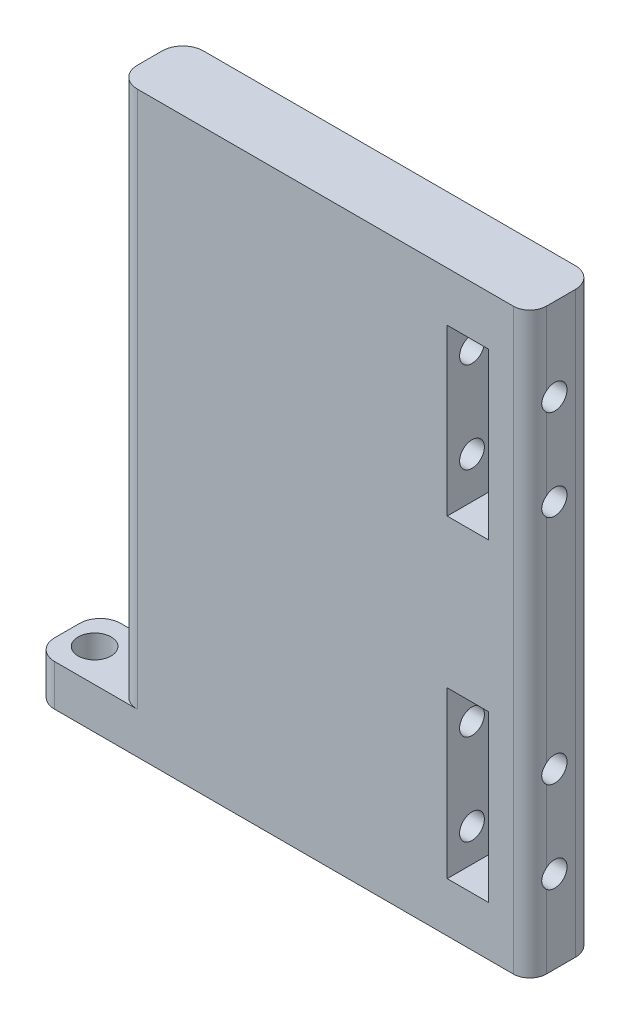
SolidWorks part; units mm, degrees
material "ABS"
ref_plane "Plano frontal" through (0, 0, 0) normal (0, 0, 1) x (1, 0, 0)
ref_plane "Plano superior" through (0, 0, 0) normal (0, 1, 0) x (1, 0, 0)
ref_plane "Plano direito" through (0, 0, 0) normal (1, 0, 0) x (0, 0, -1)
sketch "Esboço2" plane through (0, 0, 0) normal (0, 0, 1) x (1, 0, 0)
  line L1 (-67.2812, 34.8924) -> (-17.2812, 34.8924)
  line L2 (-67.2812, 34.8924) -> (-67.2812, -35.1076)
  line L3 (-67.2812, -35.1076) -> (-17.2812, -35.1076)
  line L4 (-17.2812, 34.8924) -> (-17.2812, -35.1076)
extrude "Ressalto-extrusão1" add sketch "Esboço2" along normal blind 8
sketch "Esboço3" plane through (0, -35.1076, 0) normal (0, -1, 0) x (-1, 0, 0)
  line L0 (50.5731, -0.27) -> (50.5731, -7.73) construction
  line L1 (50.5731, -7.73) -> (50.1981, -7.73) construction
  line L3 (55.6594, -4) -> (67.2812, -4) construction
  line L4 (67.2812, -8) -> (67.2812, 0) construction
  line L5 (67.2812, 0) -> (17.2812, 0) construction
  line L7 (50.5731, -7.73) -> (50.9481, -7.73) construction
  circle A5 centre (58.2812, -4) radius 0.75
  circle A7 centre (63.2812, -4) radius 0.75
  dimension "D1" = 4
  dimension "D2" = 5
  dimension "D7" = 7.46
  dimension "D8" = 0.27
  dimension "D9" = 0
extrude "Corte-extrusão1" cut sketch "Esboço3" against normal blind 30
fillet "Filete1" radius 2 1 edges at (-17.2812, -0.1076, 8)
sketch "Esboço17" plane through (0, 0, 0) normal (0, 0, -1) x (-1, 0, 0)
  line L1 (67.2812, -35.1076) -> (77.2812, -35.1076)
  line L2 (67.2812, -35.1076) -> (67.2812, -30.1076)
  line L3 (67.2812, -30.1076) -> (77.2812, -30.1076)
  line L4 (77.2812, -35.1076) -> (77.2812, -30.1076)
extrude "Ressalto-extrusão4" add sketch "Esboço17" against normal blind 8
sketch "Esboço20" plane through (0, -35.1076, 0) normal (0, -1, 0) x (1, 0, 0)
  line L0 (-77.2812, 8) -> (-19.2812, 8) construction
  circle A0 centre (-73.9512, 4) radius 2
  circle A1 centre (-63.2812, 4) radius 0.75 construction
  dimension "D1" = 4
  dimension "D2" = 10.67
extrude "Corte-extrusão9" cut sketch "Esboço20" against normal blind 8 contours A0
fillet "Filete2" radius 2.5 1 edges at (-67.2812, 2.3924, 8)
fillet "Filete3" radius 2.5 1 edges at (-67.2812, 2.3924, 0)
fillet "Filete4" radius 2.5 1 edges at (-77.2812, -32.6076, 8)
fillet "Filete5" radius 2.5 1 edges at (-77.2812, -32.6076, 0)
sketch "Esboço21" plane through (0, 0, 8) normal (0, 0, 1) x (1, 0, 0)
  line L0 (-19.2812, 34.8924) -> (-64.7812, 34.8924) construction
  line L1 (-27.2812, 28.8924) -> (-22.2812, 28.8924)
  line L2 (-27.2812, 28.8924) -> (-27.2812, 8.8924)
  line L3 (-27.2812, 8.8924) -> (-22.2812, 8.8924)
  line L4 (-22.2812, 28.8924) -> (-22.2812, 8.8924)
  line L5 (-19.2812, -35.1076) -> (-19.2812, 34.8924) construction
  line L6 (-74.7812, -35.1076) -> (-19.2812, -35.1076) construction
  line L7 (-22.2812, -29.1076) -> (-27.2812, -29.1076)
  line L8 (-22.2812, -29.1076) -> (-22.2812, -9.1076)
  line L9 (-22.2812, -9.1076) -> (-27.2812, -9.1076)
  line L10 (-27.2812, -29.1076) -> (-27.2812, -9.1076)
  dimension "D1" = 6
  dimension "D2" = 20
  dimension "D3" = 3
  dimension "D4" = 5
  dimension "D5" = 6
  dimension "D6" = 20
  dimension "D7" = 5
  dimension "D8" = 3
extrude "Corte-extrusão10" cut sketch "Esboço21" against normal through all
fillet "Filete6" radius 2.5 1 edges at (-17.2812, -0.1076, 0)
sketch "Esboço22" plane through (-17.2812, 0, 0) normal (1, 0, 0) x (0, 0, -1)
  line L0 (-6, -35.1076) -> (-2.5, -35.1076) construction
  line L1 (-6, 34.8924) -> (-2.5, 34.8924) construction
  line L2 (-8, -35.1076) -> (-8, 34.8924) construction
  circle A0 centre (-5, -25.1076) radius 1.5
  circle A1 centre (-5, -14.1076) radius 1.5
  circle A2 centre (-5, 24.8924) radius 1.5
  circle A3 centre (-5, 13.8924) radius 1.5
  dimension "D1" = 3
  dimension "D2" = 3
  dimension "D3" = 10
  dimension "D4" = 11
  dimension "D5" = 3
  dimension "D6" = 3
  dimension "D7" = 10
  dimension "D8" = 11
  dimension "D9" = 3
  dimension "D10" = 3
extrude "Corte-extrusão11" cut sketch "Esboço22" against normal blind 20
